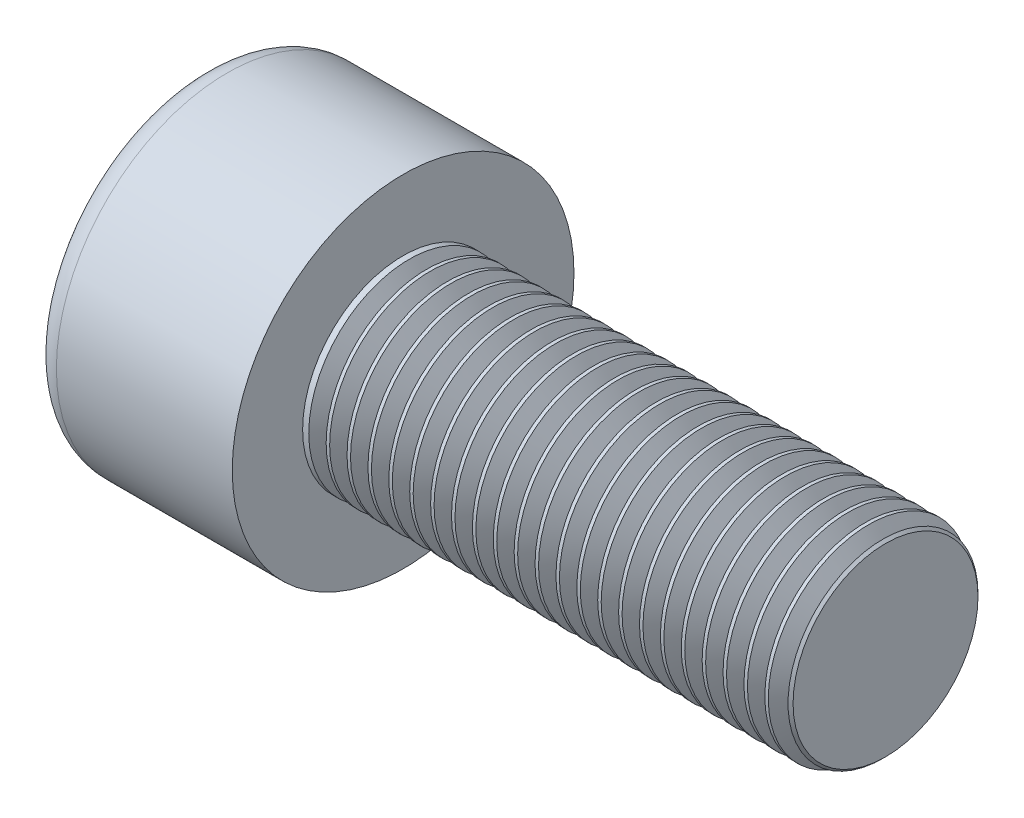
SolidWorks part; units mm, degrees
ref_plane "Front" through (0, 0, 0) normal (0, 0, 1) x (1, 0, 0)
ref_plane "Top" through (0, 0, 0) normal (0, 1, 0) x (1, 0, 0)
ref_plane "Right" through (0, 0, 0) normal (1, 0, 0) x (0, 0, -1)
sketch "Sketch1" plane through (0, 0, 0) normal (1, 0, 0) x (0, 0, -1)
  circle A0 centre (0, 0) radius 4.25
  dimension "dk" = 8.5
extrude "BaseHead" add sketch "Sketch1" along normal blind 5
sketch "Sketch2" plane through (5, 0, 0) normal (1, 0, 0) x (0, 0, -1)
  circle A0 centre (0, 0) radius 2.5
  dimension "d" = 5
extrude "BaseBody" add sketch "Sketch2" along normal blind 12
cosmetic thread "ThreadCosmetic1" [suppressed] parameters "b"=12, "D2"=4.134
sketch "Sketch3" plane through (0, 0, 0) normal (1, 0, 0) x (0, 0, -1)
  line L1 (2.3094, 0) -> (1.1547, 2)
  line L2 (1.1547, 2) -> (-1.1547, 2)
  line L3 (-1.1547, 2) -> (-2.3094, 0)
  line L4 (-2.3094, 0) -> (-1.1547, -2)
  line L5 (-1.1547, -2) -> (1.1547, -2)
  line L6 (1.1547, -2) -> (2.3094, 0)
  circle A0 centre (0, 0) radius 2 construction
  dimension "s" = 4
  dimension "e" = 4.6188
extrude "HexagonSocket" cut sketch "Sketch3" along normal blind 2.5
sketch "Sketch4" plane through (-4.1961, 0.75, 0) normal (0, 0, 1) x (-1, 0, 0)
  line L0 (-6.6961, 2.75) -> (-7.8508, 0.75)
  line L2 (-7.8508, 0.75) -> (-6.6961, 0.75)
  line L3 (-6.6961, 0.75) -> (-6.6961, 2.75)
  line L4 (-5.0351, 0.75) -> (0.839, 0.75) construction
  line L5 (-21.1961, 0.75) -> (-9.1961, 0.75) construction
  line L6 (-9.1961, 0.75) -> (-4.1961, 0.75) construction
  dimension "m" = 60
revolve "Cut-Revolve1" cut sketch "Sketch4" angle 360 about L4
fillet "HeadFillet" [suppressed] radius 0.2
fillet "TopFillet" radius 0.625 1 edges at (0, 0, -4.25)
chamfer "Chamfer1" distance 0.2 angle 45 1 edges at (17, 0, -2.5)
sketch "Sketch5" plane through (0, 0, 0) normal (0, 0, 1) x (1, 0, 0)
  line L0 (16.8, 2.125) -> (17.0165, 2.5)
  line L1 (17.0165, 2.5) -> (17.0165, 2.933)
  line L2 (17.0165, 2.933) -> (16.5835, 2.933)
  line L3 (16.5835, 2.933) -> (16.5835, 2.5)
  line L4 (16.5835, 2.5) -> (16.8, 2.125)
  line L5 (0, 0) -> (7.8886, 0) construction
  line L6 (16.8, -2.5) -> (16.8, 2.5) construction
  dimension "D1" = 5
  dimension "D2" = 0.433
revolve "Cut-Revolve10" cut sketch "Sketch5" angle 360 about L5
pattern_linear "LPattern10" count 23 spacing 0.5196 along (-1, 0, 0) of "Cut-Revolve10"
equation "\"r1@TopFillet\" = \"d@Sketch2\" / 8"
equation "\"D1@Chamfer1\" = \"r@HeadFillet\""
equation "\"D1@Sketch5\" = \"d@Sketch2\""
equation "\"D2@Sketch5\" =  ( \"d@Sketch2\" - \"D2@ThreadCosmetic1\" )  / 2"
equation "\"D3@LPattern10\" = \"D2@Sketch5\" * 1.2"
equation "\"D1@LPattern10\" = \"b@ThreadCosmetic1\" / \"D3@LPattern10\""
